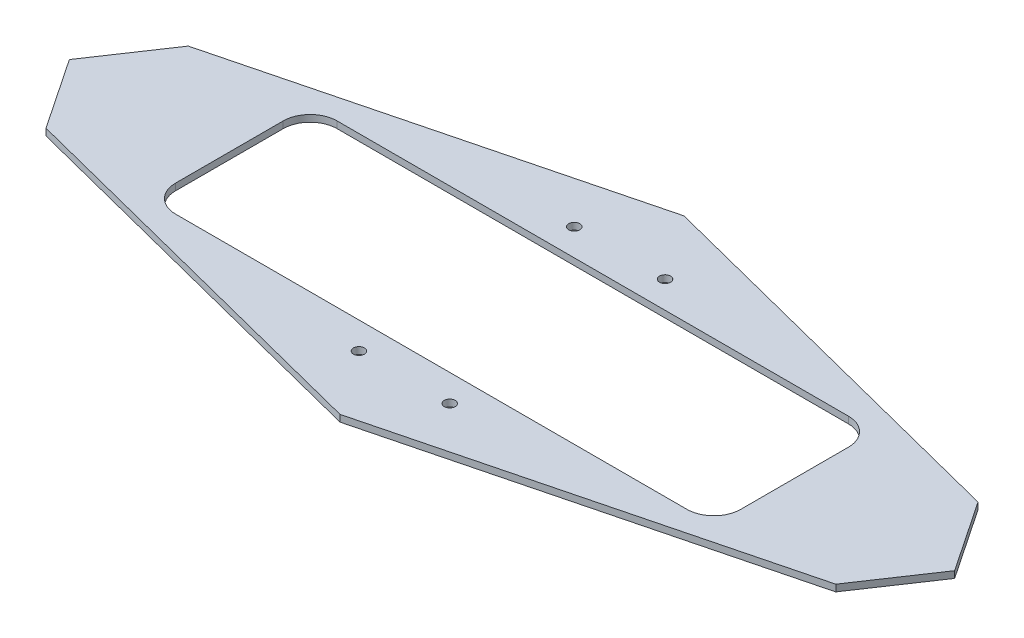
SolidWorks part; units mm, degrees
material "AISI 1020"
ref_plane "Front Plane" through (0, 0, 0) normal (0, 0, 1) x (1, 0, 0)
ref_plane "Top Plane" through (0, 0, 0) normal (0, 1, 0) x (1, 0, 0)
ref_plane "Right Plane" through (0, 0, 0) normal (1, 0, 0) x (0, 0, -1)
sketch "Sketch1" plane through (0, 0, 0) normal (0, 1, 0) x (1, 0, 0)
  line L0 (0, 0) -> (0, 457.2) construction
  line L1 (-762, 0) -> (-549.0794, 317.0112) construction
  line L2 (-762, 0) -> (0, 0) construction
  line L3 (549.0794, -317.0112) -> (-549.0794, -317.0112) construction
  line L4 (549.0794, -317.0112) -> (549.0794, 317.0112) construction
  line L5 (549.0794, 317.0112) -> (-549.0794, 317.0112) construction
  line L6 (-549.0794, -317.0112) -> (-549.0794, 317.0112) construction
  line L7 (549.0794, -317.0112) -> (-549.0794, 317.0112) construction
  line L8 (549.0794, 317.0112) -> (-549.0794, -317.0112) construction
  line L9 (-549.0794, 317.0112) -> (0, 457.2) construction
  line L10 (0, 457.2) -> (549.0794, 317.0112) construction
  line L11 (549.0794, 317.0112) -> (762, 0) construction
  line L12 (762, 0) -> (549.0794, -317.0112) construction
  line L13 (549.0794, -317.0112) -> (0, -457.2) construction
  line L14 (0, -457.2) -> (-549.0794, -317.0112) construction
  line L15 (-762, 0) -> (-549.0794, -317.0112) construction
  line L16 (-372.6919, 67.1293) -> (0, 162.2835)
  line L17 (0, 162.2835) -> (372.6919, 67.1293)
  line L18 (372.6919, 67.1293) -> (417.7793, 0)
  line L19 (417.7793, 0) -> (372.6919, -67.1293)
  line L20 (372.6919, -67.1293) -> (0, -162.2835)
  line L21 (0, -162.2835) -> (-372.6919, -67.1293)
  line L22 (-417.7793, 0) -> (-372.6919, -67.1293)
  line L23 (-417.7793, 0) -> (-372.6919, 67.1293)
  ellipse E0 centre (0, 0) end of major axis (-762, 0) minor radius 457.2 construction
  dimension "D1" = 762
  dimension "D2" = 457.2
  dimension "D3" = 30
  dimension "D4" = 285.75
extrude "Boss-Extrude1" add sketch "Sketch1" along normal mid plane 6.35
sketch "Sketch2" plane through (0, 0, 0) normal (0, 1, 0) x (1, 0, 0)
  line L0 (-266.7, 0) -> (0, 0) construction
  line L1 (241.3, 76.2) -> (-241.3, 76.2)
  line L2 (266.7, 50.8) -> (266.7, -50.8)
  line L3 (241.3, -76.2) -> (-241.3, -76.2)
  line L4 (-266.7, 50.8) -> (-266.7, -50.8)
  line L5 (266.7, 76.2) -> (-266.7, -76.2) construction
  line L6 (266.7, -76.2) -> (-266.7, 76.2) construction
  line L7 (-42.8625, 101.6) -> (42.8625, 101.6) construction
  line L13 (0, 0) -> (0, 101.6) construction
  line L19 (-42.8625, -101.6) -> (42.8625, -101.6) construction
  arc A0 (266.7, -50.8) -> (241.3, -76.2) centre (241.3, -50.8) cw
  arc A1 (241.3, 76.2) -> (266.7, 50.8) centre (241.3, 50.8) cw
  arc A2 (-241.3, -76.2) -> (-266.7, -50.8) centre (-241.3, -50.8) cw
  arc A3 (-241.3, 76.2) -> (-266.7, 50.8) centre (-241.3, 50.8) ccw
  circle A4 centre (42.8625, 101.6) radius 5.1594
  circle A5 centre (-42.8625, 101.6) radius 5.1594
  circle A10 centre (-42.8625, -101.6) radius 5.1594
  circle A11 centre (42.8625, -101.6) radius 5.1594
  point P0 (0, 0)
  point P18 (0, 101.6)
  point P19 (0, 101.6)
  point P21 (21.3663, 101.5736)
  point P28 (6.7373, 101.3764)
  point P38 (0, -101.6)
  dimension "D3" = 25.4
  dimension "D7" = 10.3187
  dimension "D1" = 533.4
  dimension "D2" = 152.4
  dimension "D4" = 85.725
  dimension "D6" = 101.6
extrude "Cut-Extrude1" cut sketch "Sketch2" against normal through all both and the other way through all
